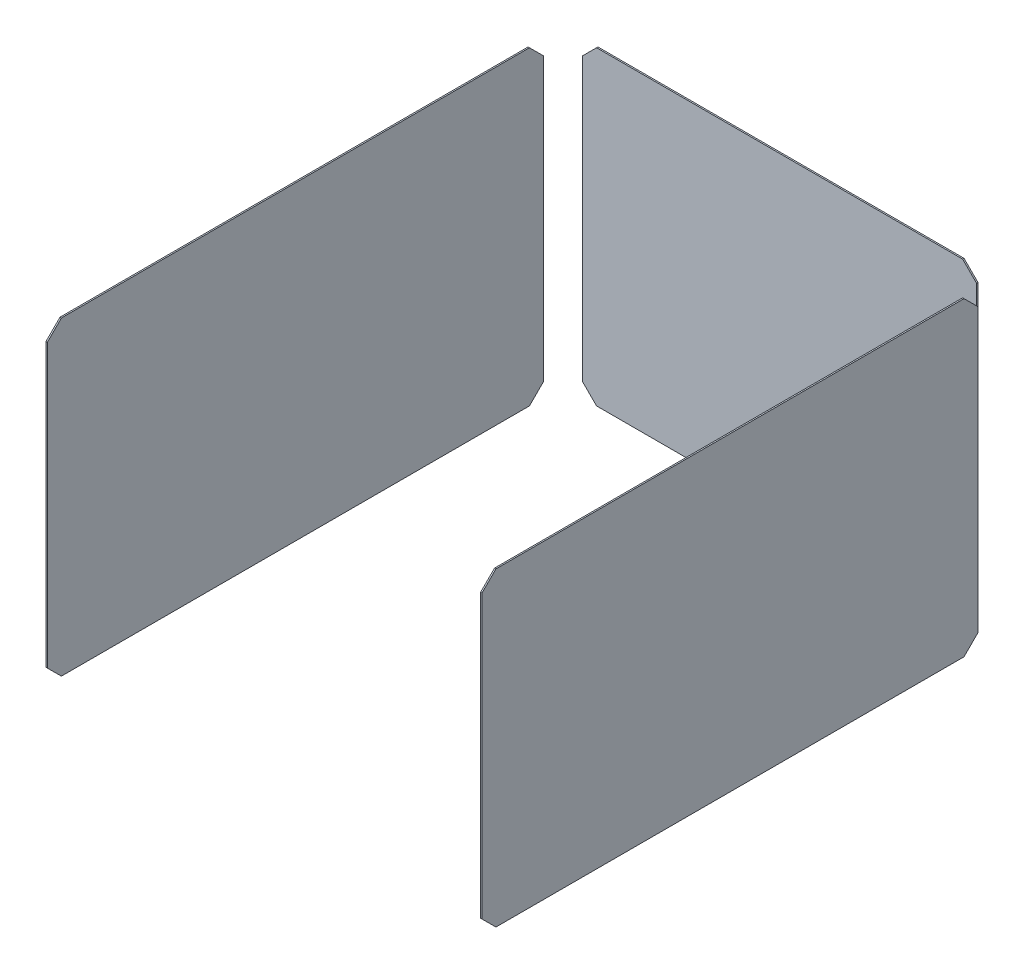
SolidWorks part; units mm, degrees
ref_plane "Plan de face" through (0, 0, 0) normal (0, 0, 1) x (1, 0, 0)
ref_plane "Plan de dessus" through (0, 0, 0) normal (0, 1, 0) x (1, 0, 0)
ref_plane "Plan de droite" through (0, 0, 0) normal (1, 0, 0) x (0, 0, -1)
sketch "Esquisse1" plane through (0, 0, 0) normal (0, 0, 1) x (1, 0, 0)
  line L1 (0, 0) -> (3100, 0)
  line L2 (0, 0) -> (0, 2500)
  line L3 (0, 2500) -> (3100, 2500)
  line L4 (3100, 0) -> (3100, 2500)
  dimension "D1" = 2500
  dimension "D2" = 3100
extrude "Extru.-Mince1" add sketch "Esquisse1" against normal blind 3700 thin
sketch "Esquisse3" plane through (0, 0, -3700) normal (0, 0, -1) x (-1, 0, 0)
  line L1 (-3100, 2500) -> (0, 2500)
  line L2 (-3100, 2500) -> (-3100, 0)
  line L3 (-3100, 0) -> (0, 0)
  line L4 (0, 2500) -> (0, 0)
extrude "Boss.-Extru.1" add sketch "Esquisse3" against normal blind 10
sketch "Esquisse2" plane through (0, 0, 0) normal (0, 0, 1) x (1, 0, 0)
  line L0 (-10, 2510) -> (-10, -10) construction
  line L1 (-60, 2560) -> (140, 2560)
  line L2 (-60, 2560) -> (-60, 2360)
  line L3 (-60, 2360) -> (140, 2360)
  line L4 (140, 2560) -> (140, 2500)
  line L5 (3110, 2510) -> (-10, 2510) construction
  line L6 (-631.6401, 1250) -> (3679.9547, 1250) construction
  line L7 (2960, 140) -> (140, 140)
  line L8 (140, 0) -> (2960, 0)
  line L9 (3160, -60) -> (2960, -60)
  line L10 (3160, -60) -> (3160, 140)
  line L11 (1550, 2697.276) -> (1550, -307.427) construction
  line L12 (3160, 140) -> (2960, 140)
  line L13 (2960, -60) -> (2960, 0)
  line L14 (140, -60) -> (140, 0)
  line L15 (-60, 140) -> (140, 140)
  line L16 (2960, 2560) -> (2960, 2500)
  line L17 (3160, 2360) -> (2960, 2360)
  line L18 (3160, 2560) -> (3160, 2360)
  line L19 (3160, 2560) -> (2960, 2560)
  line L20 (140, 2500) -> (2960, 2500)
  line L21 (0, 2500) -> (3100, 2500) construction
  line L22 (2960, 2360) -> (140, 2360)
  line L23 (-60, -60) -> (-60, 140)
  line L24 (-60, -60) -> (140, -60)
  dimension "D1" = 150
  dimension "D2" = 150
  dimension "D3" = 200
  dimension "D4" = 200
  dimension "D5" = 1260
extrude "Enlèv. mat.-Extru.1" cut sketch "Esquisse2" against normal blind 4000
sketch "Esquisse4" plane through (0, 2360, 0) normal (0, 1, 0) x (1, 0, 0)
  line L0 (-10, 3700) -> (-10, 0) construction
  line L1 (-50.9886, 3806.9959) -> (140, 3806.9959)
  line L2 (-50.9886, 3806.9959) -> (-50.9886, 3550)
  line L3 (-50.9886, 3550) -> (140, 3550)
  line L4 (140, 3806.9959) -> (140, 3550)
  line L5 (-10, 3700) -> (3110, 3700) construction
  line L6 (1550, 3866.3331) -> (1550, 3550) construction
  line L7 (2960, 3806.9959) -> (2960, 3550)
  line L8 (3150.9886, 3550) -> (2960, 3550)
  line L9 (3150.9886, 3806.9959) -> (3150.9886, 3550)
  line L10 (3150.9886, 3806.9959) -> (2960, 3806.9959)
  dimension "D1" = 150
  dimension "D2" = 150
extrude "Enlèv. mat.-Extru.2" cut sketch "Esquisse4" against normal blind 3025.2
chamfer "Chanfrein1" distance 100 angle 45 4 edges at (-5, 140, 0) (-5, 2360, 0) (-5, 140, -3550) (-5, 2360, -3550)
chamfer "Chanfrein2" distance 100 angle 45 4 edges at (140, 140, -3695) (2960, 140, -3695) (2960, 2360, -3695) (140, 2360, -3695)
chamfer "Chanfrein3" distance 100 angle 45 4 edges at (3105, 2360, 0) (3105, 140, -3550) (3105, 140, 0) (3105, 2360, -3550)
